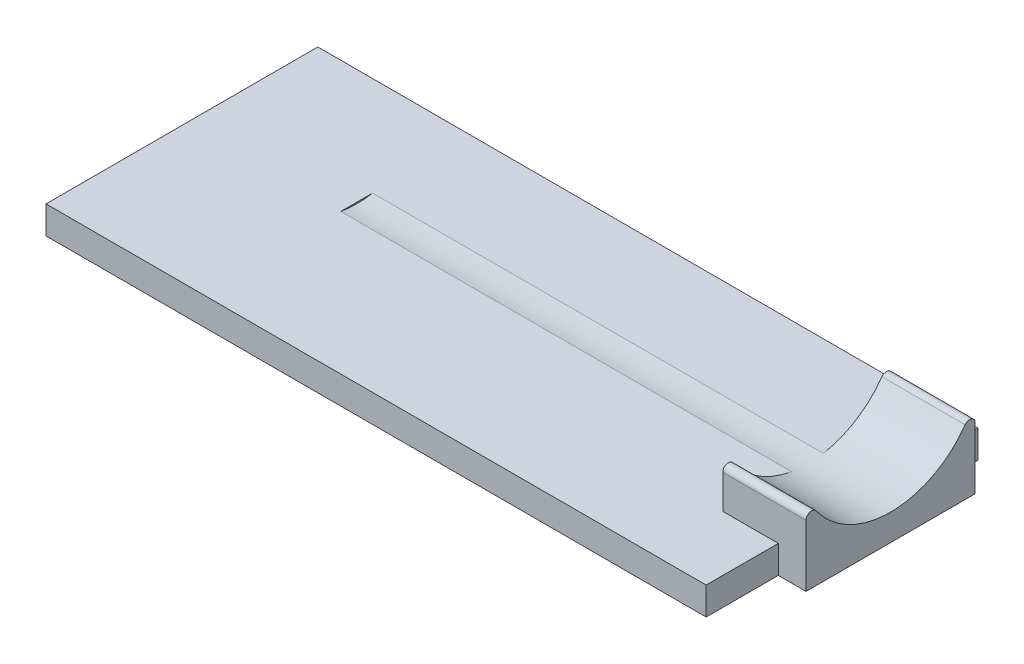
SolidWorks part; units mm, degrees
ref_plane "Front Plane" through (0, 0, 0) normal (0, 0, 1) x (1, 0, 0)
ref_plane "Top Plane" through (0, 0, 0) normal (0, 1, 0) x (1, 0, 0)
ref_plane "Right Plane" through (0, 0, 0) normal (1, 0, 0) x (0, 0, -1)
sketch "Sketch1" plane through (0, 0, 0) normal (0, 1, 0) x (1, 0, 0)
  line L1 (0, 0) -> (-23.8, 0)
  line L2 (0, 0) -> (0, 9.8)
  line L3 (0, 9.8) -> (-23.8, 9.8)
  line L4 (-23.8, 0) -> (-23.8, 9.8)
  dimension "D1" = 23.8
  dimension "D2" = 9.8
extrude "Boss-Extrude1" add sketch "Sketch1" along normal blind 1
sketch "Sketch2" plane through (0, 1, 0) normal (0, 1, 0) x (1, 0, 0)
  line L0 (0, 9.8) -> (-23.8, 9.8) construction
  line L2 (1, 2.6) -> (-2, 2.6)
  line L3 (-2, 2.6) -> (-2, 8.7)
  line L4 (-2, 8.7) -> (1, 8.7)
  line L5 (1, 8.7) -> (1, 2.6)
  line L7 (0, 9.8) -> (0, 8.7) construction
  line L9 (0, 0) -> (0, 9.8) construction
  dimension "D1" = 3
  dimension "D2" = 6.1
  dimension "D3" = 1.1
  dimension "D4" = 1
extrude "Boss-Extrude2" add sketch "Sketch2" along normal blind 3.25
sketch "Sketch4" plane through (0, 1, 0) normal (0, -1, 0) x (1, 0, 0)
  line L1 (0, -2.6) -> (1, -2.6)
  line L2 (0, -2.6) -> (0, -8.7)
  line L3 (0, -8.7) -> (1, -8.7)
  line L4 (1, -2.6) -> (1, -8.7)
extrude "Boss-Extrude3" add sketch "Sketch4" along normal up to surface (1 mm away) up to face at (-11.9, 0, -4.9)
sketch "Sketch3" plane through (1, 0, 0) normal (1, 0, 0) x (0, 0, -1)
  line L0 (2.35, 4.25) -> (8.95, 4.25) construction
  line L1 (2.6, 4.25) -> (8.7, 4.25) construction
  circle A0 centre (5.65, 4.25) radius 3.3
  point P2 (5.85, 4.25)
  dimension "D1" = 6.6
extrude "Cut-Extrude1" cut sketch "Sketch3" against normal blind 19.25
fillet "Fillet1" radius 0.2 2 edges at (-0.5, 2.99, -8.7) (-0.5, 2.99, -2.6)
